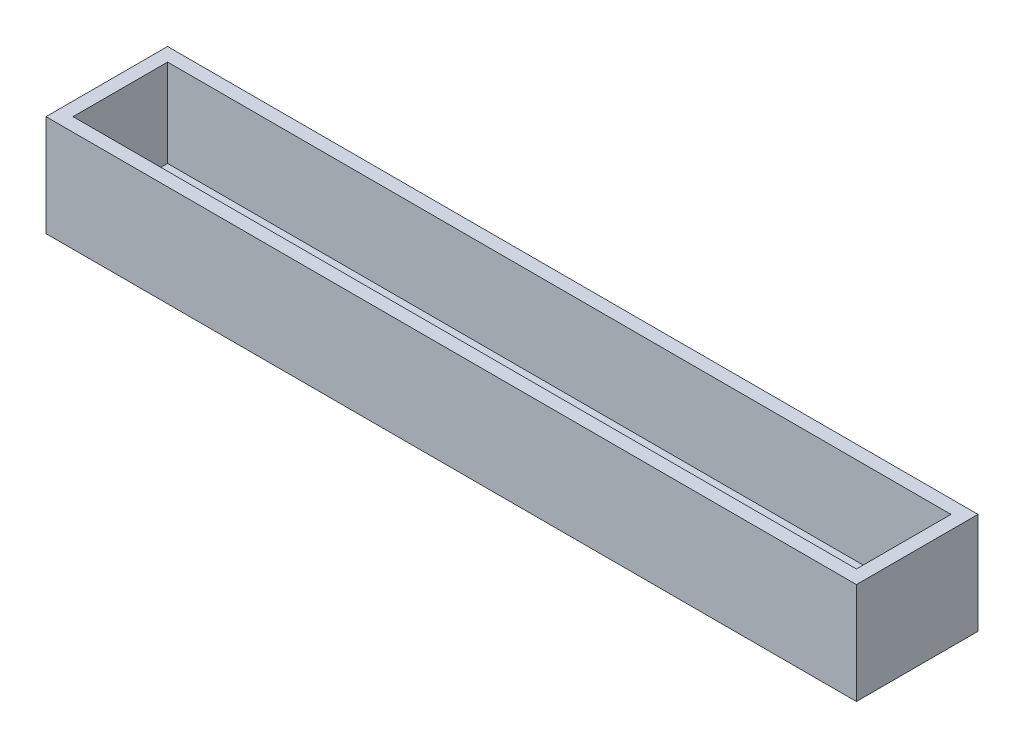
SolidWorks part; units mm, degrees
ref_plane "Plan de face" through (0, 0, 0) normal (0, 0, 1) x (1, 0, 0)
ref_plane "Plan de dessus" through (0, 0, 0) normal (0, 1, 0) x (1, 0, 0)
ref_plane "Plan de droite" through (0, 0, 0) normal (1, 0, 0) x (0, 0, -1)
sketch "Esquisse1" plane through (0, 0, 0) normal (0, 1, 0) x (1, 0, 0)
  line L1 (0, 0) -> (60, 0)
  line L2 (0, 0) -> (0, 9)
  line L3 (0, 9) -> (60, 9)
  line L4 (60, 0) -> (60, 9)
  dimension "D1" = 60
  dimension "D2" = 9
extrude "Boss.-Extru.1" add sketch "Esquisse1" along normal blind 1
sketch "Esquisse2" plane through (0, 1, 0) normal (0, 1, 0) x (1, 0, 0)
  line L0 (60, 9) -> (0, 9) construction
  line L1 (1, 8) -> (59, 8)
  line L2 (1, 8) -> (1, 1)
  line L3 (1, 1) -> (59, 1)
  line L4 (59, 8) -> (59, 1)
  line L5 (60, 0) -> (60, 9) construction
  line L6 (0, 0) -> (60, 0) construction
  line L7 (0, 9) -> (0, 0) construction
  line L9 (0, 0) -> (60, 0)
  line L10 (0, 0) -> (0, 9)
  line L11 (0, 9) -> (60, 9)
  line L12 (60, 0) -> (60, 9)
  dimension "D1" = 1
  dimension "D2" = 1
  dimension "D3" = 1
  dimension "D4" = 1
extrude "Boss.-Extru.2" add sketch "Esquisse2" along normal blind 6.5
sketch "Esquisse3" plane through (0, 0, 0) normal (0, -1, 0) x (1, 0, 0)
  line L0 (0, -9) -> (0, 0) construction
  line L1 (56, -6) -> (4, -6)
  line L2 (56, -6) -> (56, -3)
  line L3 (56, -3) -> (4, -3)
  line L4 (4, -6) -> (4, -3)
  line L5 (0, 0) -> (60, 0) construction
  point P8 (4, -4.5)
  point P9 (0, -4.5)
  point P12 (30, 0)
  point P13 (30, -3)
  dimension "D1" = 52
  dimension "D2" = 3
extrude "Enlèv. mat.-Extru.1" cut sketch "Esquisse3" against normal through all
